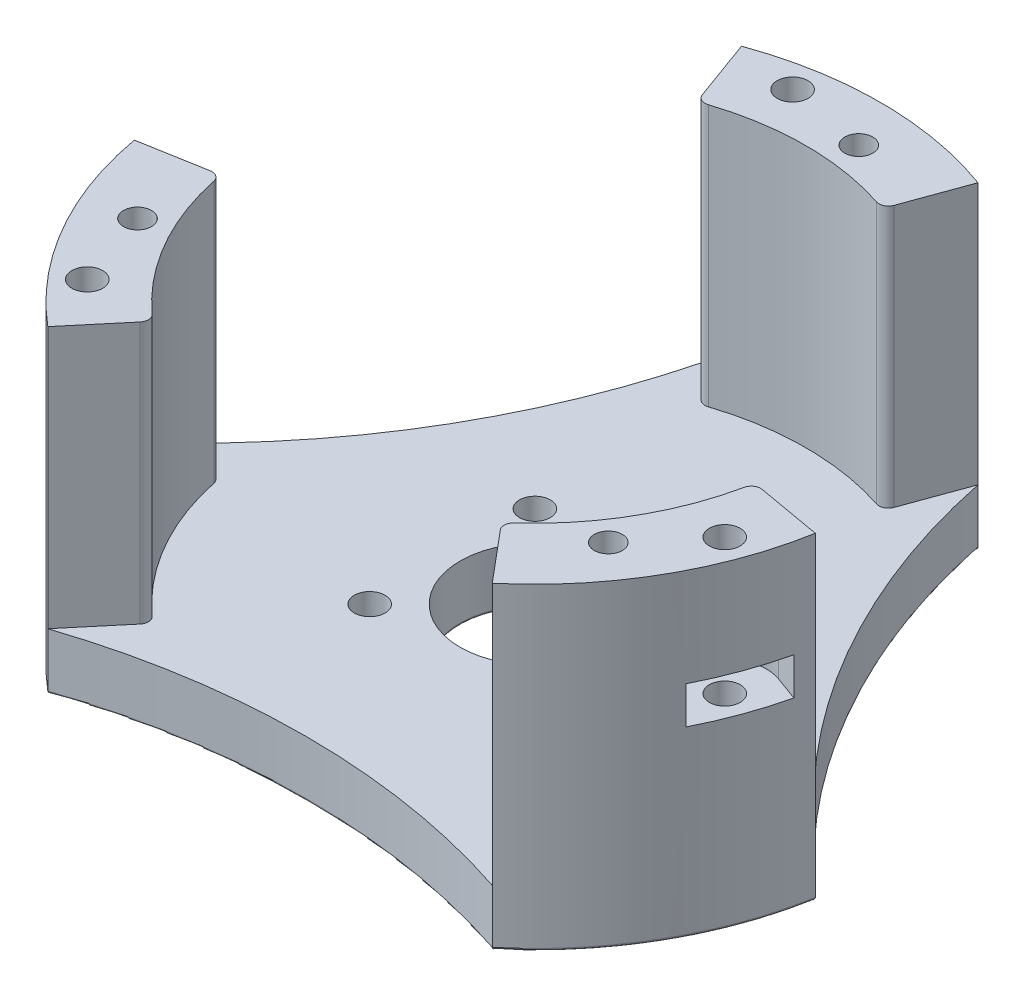
SolidWorks part; units mm, degrees
ref_plane "Front Plane" through (0, 0, 0) normal (0, 0, 1) x (1, 0, 0)
ref_plane "Top Plane" through (0, 0, 0) normal (0, 1, 0) x (1, 0, 0)
ref_plane "Right Plane" through (0, 0, 0) normal (1, 0, 0) x (0, 0, -1)
sketch "Sketch1" plane through (0, 0, 0) normal (0, 1, 0) x (1, 0, 0)
  line L1 (-8.8388, -8.8388) -> (8.8388, -8.8388) construction
  line L2 (-8.8388, -8.8388) -> (-8.8388, 8.8388) construction
  line L3 (-8.8388, 8.8388) -> (8.8388, 8.8388) construction
  line L4 (8.8388, -8.8388) -> (8.8388, 8.8388) construction
  line L5 (-8.8388, -8.8388) -> (8.8388, 8.8388) construction
  line L6 (-8.8388, 8.8388) -> (8.8388, -8.8388) construction
  circle A0 centre (0, 0) radius 37
  circle A1 centre (-8.8388, 8.8388) radius 1.65
  circle A2 centre (8.8388, 8.8388) radius 1.65
  circle A3 centre (8.8388, -8.8388) radius 1.65
  circle A4 centre (-8.8388, -8.8388) radius 1.65
  dimension "D1" = 74
  dimension "D4" = 3.3
  dimension "D2" = 12.5
extrude "Boss-Extrude1" add sketch "Sketch1" along normal blind 6
sketch "Sketch2" plane through (0, 6, 0) normal (0, 1, 0) x (1, 0, 0)
  line L0 (-12.6547, 34.7686) -> (0, 0) construction
  line L1 (0, 0) -> (12.6547, 34.7686) construction
  line L2 (0, -1000) -> (0, 49000) construction
  line L3 (-12.6547, 34.7686) -> (-9.9186, 27.2511)
  line L4 (9.9186, 27.2511) -> (12.6547, 34.7686)
  line L5 (2.789, 31.8782) -> (0, 0) construction
  arc A0 (12.6547, 34.7686) -> (-12.6547, 34.7686) centre (0, 0) ccw
  circle A1 centre (0, 0) radius 37 construction
  arc A2 (9.9186, 27.2511) -> (-9.9186, 27.2511) centre (0, 0) ccw
  circle A3 centre (2.789, 31.8782) radius 1.5
  dimension "D1" = 8
  dimension "D5" = 3
  dimension "D2" = 20
  dimension "D3" = 20
  dimension "D4" = 32
  dimension "D6" = 5
extrude "Boss-Extrude2" add sketch "Sketch2" along normal blind 28
sketch "Sketch16" plane through (0, 34, 0) normal (0, 1, 0) x (1, 0, 0)
  circle A0 centre (2.789, 31.8782) radius 1.5
  circle A1 centre (2.789, 31.8782) radius 1.5 construction
extrude "Cut-Extrude9" cut sketch "Sketch16" against normal through all
pattern_circular "CirPattern1" count 3 over 360 about axis through (0, 0, 0) along (0, 1, 0) of "Boss-Extrude2", "Cut-Extrude9"
sketch "Sketch3" plane through (0, 6, 0) normal (0, 1, 0) x (1, 0, 0)
  circle A0 centre (0, 0) radius 8
  dimension "D1" = 16
extrude "Cut-Extrude1" cut sketch "Sketch3" against normal blind 10
sketch "Sketch4" plane through (0, 0, 0) normal (0, -1, 0) x (1, 0, 0)
  circle A0 centre (8.8388, 8.8388) radius 3.5
  circle A1 centre (8.8388, -8.8388) radius 3.5
  circle A2 centre (-8.8388, -8.8388) radius 3.5
  circle A3 centre (-8.8388, 8.8388) radius 3.5
  dimension "D1" = 7
extrude "Cut-Extrude2" cut sketch "Sketch4" against normal blind 3
sketch "Sketch5" plane through (0, 6, 0) normal (0, 1, 0) x (1, 0, 0)
  circle A1 centre (86.6025, 50) radius 75.5001
  dimension "D1" = 100
extrude "Cut-Extrude3" cut sketch "Sketch5" against normal through all
pattern_circular "CirPattern2" count 3 over 360 about axis through (0, 0, 0) along (0, 1, 0) of "Cut-Extrude3"
fillet "Fillet1" radius 0.25 14 edges at (-8.8388, 0, -12.3388) (8.8388, 0, -12.3388) (8.8388, 0, 5.3388) (0, 0, -37) (21.2175, 0, -12.2499) (-32.0429, 0, 18.5) (32.0429, 0, 18.5) (0, 0, 24.4999) (-21.2175, 0, -12.2499) (2.789, 0, -30.3782) (-27.7028, 0, 12.7738) (24.9138, 0, 17.6044) (0, 0, 8) (-8.8388, 0, 5.3388)
fillet "Fillet2" radius 1 6 edges at (28.5594, 20, 5.0358) (9.9186, 20, -27.2511) (-9.9186, 20, -27.2511) (18.6408, 20, 22.2153) (-28.5594, 20, 5.0358) (-18.6408, 20, 22.2153)
sketch "Sketch6" plane through (0, 34, 0) normal (0, 1, 0) x (1, 0, 0)
  line L0 (0, 32) -> (0, 0) construction
  line L1 (0, 0) -> (-29.0018, -13.5238) construction
  line L2 (0, 0) -> (26.2129, -18.3544) construction
  circle A0 centre (0, 0) radius 6
  circle A1 centre (14.7447, -10.3244) radius 12
  circle A2 centre (0, 18) radius 12
  circle A3 centre (-16.3135, -7.6071) radius 12
  circle A4 centre (0, 0) radius 32 construction
  point P7 (14.7447, -10.3244)
  point P9 (0, 18)
  point P10 (-16.3135, -7.6071)
  dimension "D1" = 12
  dimension "D2" = 24
sketch "Sketch7" plane through (0, 34, 0) normal (0, 1, 0) x (1, 0, 0)
  circle A0 centre (0, 0) radius 18
  circle A1 centre (0, 0) radius 13
  dimension "D1" = 26
  dimension "D2" = 5
ref_plane "Plane1" through (0, 23.5, 0) normal (0, 1, 0) x (1, 0, 0)
sketch "Sketch9" plane through (0, 23.5, 0) normal (0, 1, 0) x (1, 0, 0)
  line L0 (-5.904, 33.4835) -> (0, 0) construction
  line L1 (-13.5581, 36.1956) -> (-5.7547, 37.5715) construction
  line L2 (0, 32) -> (0, 0) construction
  line L3 (-23.4143, 33.4422) -> (49216.9734, 8715.8511) construction
  circle A0 centre (-5.904, 33.4835) radius 4 construction
  circle A1 centre (-5.904, 33.4835) radius 1.65
  arc A2 (12.6547, 34.7686) -> (-12.6547, 34.7686) centre (0, 0) ccw construction
  dimension "D1" = 8
  dimension "D2" = 3.3
  dimension "D3" = 1
  dimension "D4" = 10
extrude "Cut-Extrude4" cut sketch "Sketch9" against normal through all and the other way through all
sketch "Sketch10" plane through (0, 23.5, 0) normal (0, 1, 0) x (1, 0, 0)
  line L0 (-11.2039, 37.6261) -> (-10.3357, 32.702)
  line L1 (-2.3406, 39.1889) -> (-1.4724, 34.2649)
  line L2 (-5.904, 33.4835) -> (0, 0) construction
  line L3 (-11.2039, 37.6261) -> (-2.3406, 39.1889)
  line L4 (-13.5581, 36.1956) -> (-5.7547, 37.5715) construction
  arc A0 (-10.3357, 32.702) -> (-1.4724, 34.2649) centre (-5.904, 33.4835) ccw
  dimension "D1" = 9
  dimension "D2" = 1
extrude "Cut-Extrude5" cut sketch "Sketch10" against normal blind 4
pattern_circular "CirPattern3" count 3 over 360 about axis through (0, 0, 0) along (0, 1, 0) of "Cut-Extrude4", "Cut-Extrude5"
